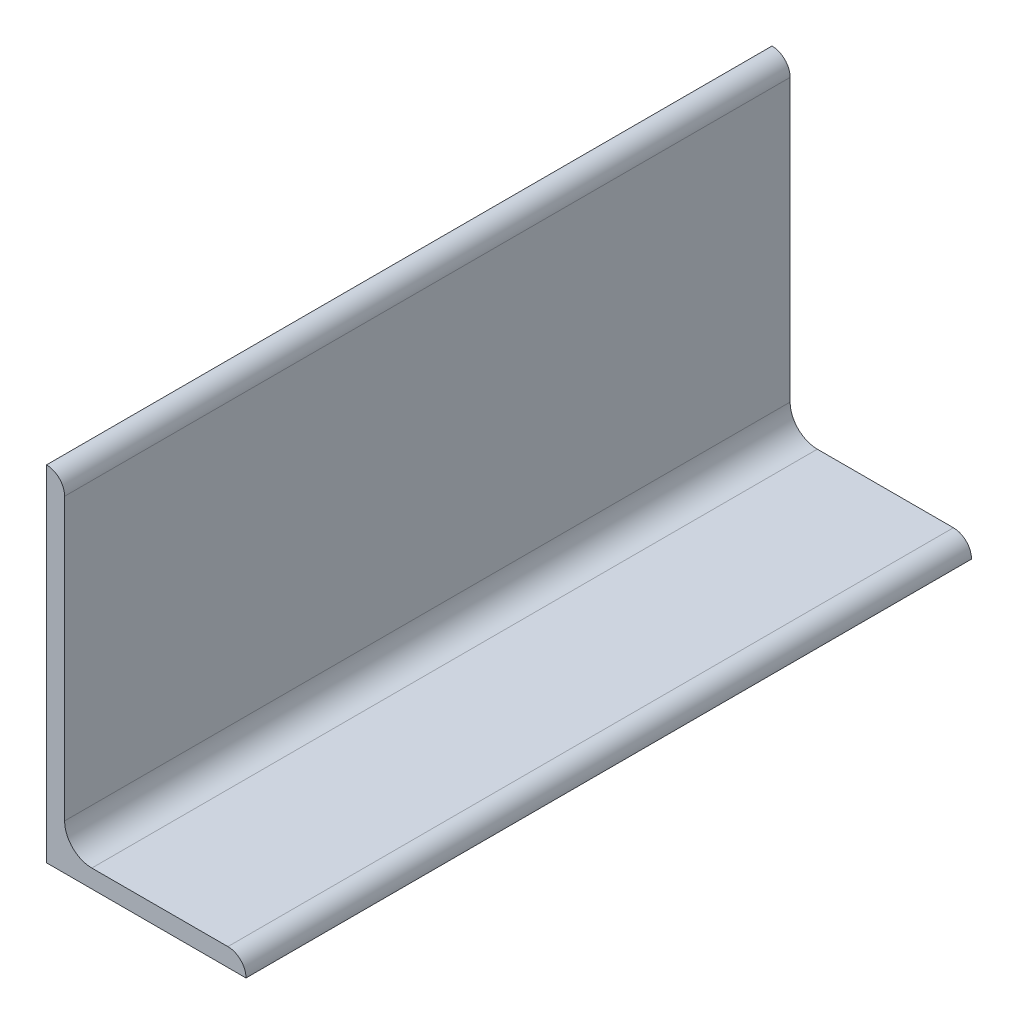
SolidWorks part; units mm, degrees
material "5052-H36"
ref_plane "Plane1" through (0, 0, 0) normal (0, 0, 1) x (1, 0, 0)
ref_plane "Plane2" through (0, 0, 0) normal (0, 1, 0) x (1, 0, 0)
ref_plane "Plane3" through (0, 0, 0) normal (1, 0, 0) x (0, 0, -1)
sketch "Sketch1" plane through (0, 0, 0) normal (0, 0, 1) x (1, 0, 0)
  line L0 (0, 0) -> (0, 60.325)
  line L1 (0, 60.325) -> (0.0051, 60.325)
  line L2 (3.175, 57.1551) -> (3.175, 7.9375)
  line L3 (7.9375, 3.175) -> (31.7551, 3.175)
  line L4 (34.925, 0.0051) -> (34.925, 0)
  line L5 (34.925, 0) -> (0, 0)
  arc A0 (34.925, 0.0051) -> (31.7551, 3.175) centre (31.7551, 0.0051) ccw
  arc A1 (0.0051, 60.325) -> (3.175, 57.1551) centre (0.0051, 57.1551) cw
  arc A2 (7.9375, 3.175) -> (3.175, 7.9375) centre (7.9375, 7.9375) cw
  circle A3 centre (0, 0) radius 3.175 construction
  dimension "D2" = 0.0051
  dimension "Radius_1" = 4.7625
  dimension "Radius_2" = 3.175
  dimension "D1" = 3.175
  dimension "V_leg" = 60.325
  dimension "H_leg" = 34.925
  dimension "Thickness" = 3.175
  dimension "Flat_wid" = 0.0051
extrude "BaseSteelAngle" add sketch "Sketch1" along normal mid plane 127
equation "\"Flat_wid@Sketch1\" = ((sgn(\"Thickness@Sketch1\" - \"Radius_2@Sketch1\") +1)*(\"Thickness@Sketch1\" - \"Radius_2@Sketch1\"))/2 +0.0002"
equation "\"D1@Sketch1\" = \"Thickness@Sketch1\""
equation "\"D2@Sketch1\" = \"Flat_wid@Sketch1\""
